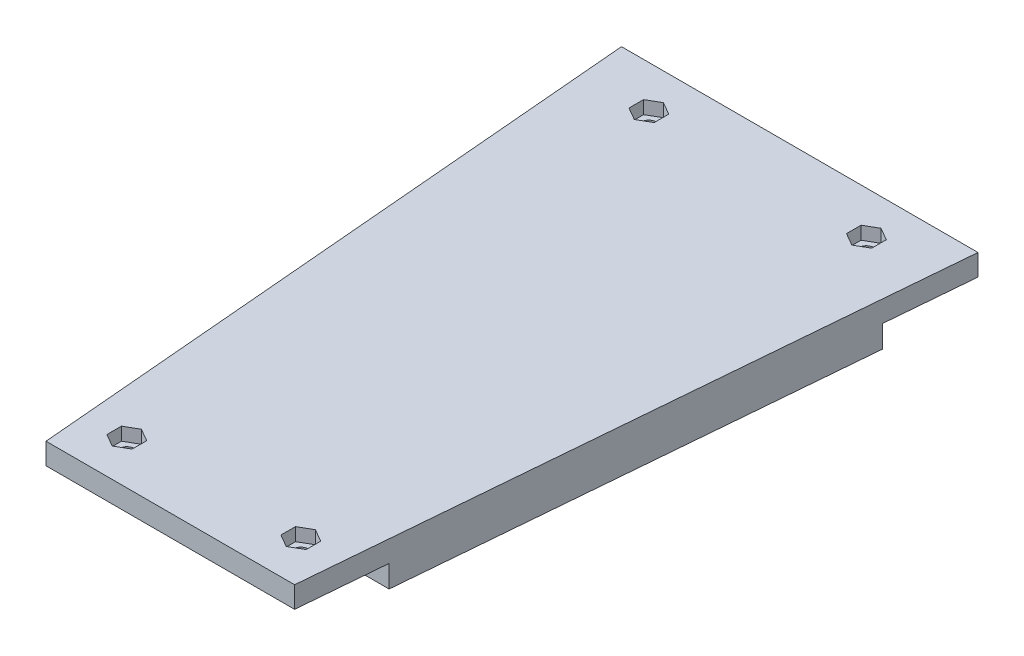
SolidWorks part; units mm, degrees
ref_plane "Front Plane" through (0, 0, 0) normal (0, 0, 1) x (1, 0, 0)
ref_plane "Top Plane" through (0, 0, 0) normal (0, 1, 0) x (1, 0, 0)
ref_plane "Right Plane" through (0, 0, 0) normal (1, 0, 0) x (0, 0, -1)
sketch "Sketch1" plane through (0, 0, 0) normal (0, 1, 0) x (1, 0, 0)
  circle A0 centre (0, 0) radius 50
extrude "Boss-Extrude1" add sketch "Sketch1" along normal blind 10
sketch "Sketch2" plane through (0, 10, 0) normal (0, 1, 0) x (1, 0, 0)
  circle A0 centre (0, 0) radius 20
extrude "Cut-Extrude1" cut sketch "Sketch2" against normal blind 5
sketch "Sketch7" plane through (0, 0, 0) normal (0, -1, 0) x (1, 0, 0)
  line L0 (10.1404, -5.8546) -> (10.1404, -9.1454)
  line L1 (0, 11.7091) -> (2.85, 13.3546)
  line L2 (2.85, 13.3546) -> (2.85, 16.6454)
  line L3 (2.85, 16.6454) -> (0, 18.2909)
  line L4 (0, 18.2909) -> (-2.85, 16.6454)
  line L5 (-2.85, 16.6454) -> (-2.85, 13.3546)
  line L6 (-2.85, 13.3546) -> (0, 11.7091)
  line L7 (10.1404, -9.1454) -> (12.9904, -10.7909)
  line L8 (12.9904, -10.7909) -> (15.8404, -9.1454)
  line L9 (15.8404, -9.1454) -> (15.8404, -5.8546)
  line L10 (15.8404, -5.8546) -> (12.9904, -4.2091)
  line L11 (12.9904, -4.2091) -> (10.1404, -5.8546)
  line L12 (-10.1404, -5.8546) -> (-12.9904, -4.2091)
  line L13 (-12.9904, -4.2091) -> (-15.8404, -5.8546)
  line L14 (-15.8404, -5.8546) -> (-15.8404, -9.1454)
  line L15 (-15.8404, -9.1454) -> (-12.9904, -10.7909)
  line L16 (-12.9904, -10.7909) -> (-10.1404, -9.1454)
  line L17 (-10.1404, -9.1454) -> (-10.1404, -5.8546)
  circle A0 centre (0, 0) radius 15
  circle A1 centre (0, 15) radius 2.85 construction
  point P25 (0, 0)
  dimension "D1" = 3
extrude "Cut-Extrude6" cut sketch "Sketch7" against normal blind 3 contours A0 L2 L3 L4 L5 | L2 A0 L5 L6 L1 | L13 L14 L15 L16 L17 L12 | L10 L11 L0 L7 L8 L9
sketch "Sketch8" plane through (0, 0, 0) normal (0, -1, 0) x (1, 0, 0)
  line L0 (-2.85, 15) -> (2.85, 15) construction
  line L1 (-2.85, 16.6454) -> (-2.85, 13.3546) construction
  line L2 (2.85, 13.3546) -> (2.85, 16.6454) construction
  circle A0 centre (0, 15) radius 1.7
  circle A1 centre (12.9904, -7.5) radius 1.7
  circle A2 centre (-12.9904, -7.5) radius 1.7
  point P14 (0, 0)
  dimension "D1" = 3
extrude "Cut-Extrude7" cut sketch "Sketch8" against normal blind 10
sketch "Sketch9" plane through (0, 0, 0) normal (0, -1, 0) x (1, 0, 0)
  line L1 (-50, 0) -> (50, 0)
  line L2 (-50, 0) -> (-50, 350)
  line L3 (-50, 350) -> (50, 350)
  line L4 (50, 0) -> (50, 350)
  circle A0 centre (0, 0) radius 50 construction
  circle A1 centre (0, 0) radius 50
  circle M23 centre (0, 0) radius 50
  dimension "D1" = 350
extrude "Boss-Extrude3" add sketch "Sketch9" against normal blind 10 separate body contours L4 L3 L2 M23
sketch "Sketch10" plane through (0, 0, 0) normal (0, -1, 0) x (1, 0, 0)
  line L0 (0, 350) -> (0, 0) construction
  line L1 (-50, 350) -> (50, 350) construction
  line L3 (-10.5, 299) -> (10.5, 299)
  line L4 (-10.5, 299) -> (-10.5, 340)
  line L5 (-10.5, 340) -> (10.5, 340)
  line L6 (10.5, 299) -> (10.5, 340)
  line L7 (-10.5, 299) -> (10.5, 340) construction
  line L8 (-10.5, 340) -> (10.5, 299) construction
  point P5 (0, 319.5)
  dimension "D1" = 41
  dimension "D2" = 21
  dimension "D3" = 10
extrude "Cut-Extrude8" cut sketch "Sketch10" against normal blind 10
sketch "Sketch11" plane through (0, 0, 0) normal (0, -1, 0) x (1, 0, 0)
  line L0 (-10.5, 340) -> (-10.5, 299) construction
  line L1 (-10.5, 292.5) -> (10.5, 292.5)
  line L2 (-10.5, 292.5) -> (-10.5, 346.5)
  line L3 (-10.5, 346.5) -> (10.5, 346.5)
  line L4 (10.5, 292.5) -> (10.5, 346.5)
  line L5 (-10.5, 292.5) -> (10.5, 346.5) construction
  line L6 (-10.5, 346.5) -> (10.5, 292.5) construction
  line L7 (-10.5, 340) -> (-10.5, 299)
  line L8 (10.5, 340) -> (-10.5, 340) construction
  line L9 (10.5, 340) -> (-10.5, 340)
  point P0 (0, 319.5)
  point P8 (-10.5, 319.5)
  point P9 (-10.5, 319.5)
  point P11 (0, 346.5)
  point P12 (0, 340)
  line M6 (10.5, 299) -> (-10.5, 299)
  line M8 (-10.5, 340) -> (10.5, 340)
  dimension "D1" = 54
  dimension "D2" = 21
extrude "Cut-Extrude9" cut sketch "Sketch11" against normal blind 1.5 contours L4 L3 L2 M8 | L1 L4 L2 M6
sketch "Sketch12" plane through (0, 1.5, 0) normal (0, -1, 0) x (1, 0, 0)
  line L0 (-5, 343.75) -> (5, 343.75) construction
  line L1 (-10.5, 340) -> (10.5, 340) construction
  line L2 (-10.5, 346.5) -> (10.5, 346.5) construction
  line L3 (-10.5, 346.5) -> (10.5, 346.5)
  line L4 (-10.5, 319.5) -> (10.5, 319.5) construction
  line L5 (-10.5, 346.5) -> (-10.5, 292.5) construction
  line L6 (10.5, 292.5) -> (10.5, 346.5) construction
  circle A0 centre (-5, 343.75) radius 1.7
  circle A1 centre (5, 343.75) radius 1.7
  circle A2 centre (-5, 295.25) radius 1.7
  circle A3 centre (5, 295.25) radius 1.7
  point P3 (0, 343.75)
  point P9 (0, 346.5)
  dimension "D1" = 3.75
extrude "Cut-Extrude10" cut sketch "Sketch12" against normal blind 9 contours A0 | A1 | A2 | A3
sketch "Sketch13" plane through (0, 0, 0) normal (0, -1, 0) x (1, 0, 0)
  line L0 (-50, 0) -> (-20, 350)
  line L1 (0, 350) -> (0, 0) construction
  line L2 (50, 0) -> (20, 350)
  line L3 (50, 0) -> (50, 350)
  line L4 (50, 350) -> (-50, 350)
  line L5 (-50, 350) -> (-50, 0)
  line L6 (50, 0) -> (50, 350)
  line L7 (50, 350) -> (-50, 350)
  line L8 (-50, 350) -> (-50, 0)
  arc A1 (50, 0) -> (-50, 0) centre (0, 0) ccw
  arc A2 (50, 0) -> (-50, 0) centre (0, 0) ccw
  arc M7 (-50, 0) -> (50, 0) centre (0, 0) cw
  line M8 (50, 0) -> (50, 350)
  line M9 (50, 350) -> (-50, 350)
  line M10 (-50, 350) -> (-50, 0)
  dimension "D2" = 20
  dimension "D1" = 0
extrude "Cut-Extrude11" cut sketch "Sketch13" against normal blind 10 contours L0 M7 M9 M10 | L2 M7 M8 M9
sketch "Sketch14" plane through (0, 0, 0) normal (0, -1, 0) x (1, 0, 0)
  line L0 (0, 0) -> (0, 125) construction
  line L2 (-64.1644, 125) -> (57.7014, 125)
  line L3 (-64.1644, 125) -> (-64.1644, 375)
  line L4 (-64.1644, 375) -> (57.7014, 375)
  line L5 (57.7014, 125) -> (57.7014, 375)
  point P7 (0, 0)
  dimension "D1" = 125
  dimension "D2" = 250
sketch "Sketch15" plane through (0, 10, 0) normal (0, 1, 0) x (1, 0, 0)
  line L1 (57.7014, -125) -> (-74.0337, -125)
  line L2 (57.7014, -125) -> (57.7014, 54.2666)
  line L3 (57.7014, 54.2666) -> (-74.0337, 54.2666)
  line L4 (-74.0337, -125) -> (-74.0337, 54.2666)
extrude "Cut-Extrude12" cut sketch "Sketch15" against normal blind 79
sketch "Sketch16" plane through (0, 10, 0) normal (0, 1, 0) x (1, 0, 0)
  line L0 (-40.9724, -105.3222) -> (-37.599, -144.6778)
  line L2 (-39.2857, -125) -> (-20, -350) construction
  line L3 (0, -125) -> (0, -150.7956) construction
  line L4 (40.9724, -105.3222) -> (37.599, -144.6778)
  line L5 (-40.9724, -105.3222) -> (40.9724, -105.3222)
  line L9 (20, -350) -> (39.2857, -125)
  line L10 (39.2857, -125) -> (-39.2857, -125)
  line L11 (-39.2857, -125) -> (-20, -350)
  line L12 (-20, -350) -> (20, -350)
  line L13 (20, -350) -> (39.2857, -125)
  line L14 (39.2857, -125) -> (-39.2857, -125)
  line L15 (-39.2857, -125) -> (-20, -350)
  line L16 (-20, -350) -> (20, -350)
  point P4 (-39.2857, -125)
  line M18 (39.2857, -125) -> (-39.2857, -125)
  dimension "D1" = 0
extrude "Boss-Extrude4" add sketch "Sketch16" against normal blind 4.9 contours L5 L0 L14 L4 M18
sketch "Sketch17" plane through (0, 5.1, 0) normal (0, -1, 0) x (1, 0, 0)
  line L0 (0, 125) -> (0, 115) construction
  line L1 (0, 0) -> (0, 125) construction
  line L2 (-25, 115) -> (25, 115) construction
  circle A0 centre (-25, 115) radius 1.7
  circle A1 centre (25, 115) radius 1.7
  point P8 (0, 115)
extrude "Cut-Extrude13" cut sketch "Sketch17" against normal blind 10
sketch "Sketch18" plane through (0, 10, 0) normal (0, 1, 0) x (1, 0, 0)
  line L0 (0, -105.3222) -> (0, -125) construction
  line L1 (-25, -111.6514) -> (-27.9, -113.3257)
  line L2 (-27.9, -113.3257) -> (-27.9, -116.6743)
  line L3 (-27.9, -116.6743) -> (-25, -118.3486)
  line L4 (-25, -118.3486) -> (-22.1, -116.6743)
  line L5 (-22.1, -116.6743) -> (-22.1, -113.3257)
  line L6 (-22.1, -113.3257) -> (-25, -111.6514)
  line L7 (-40.9724, -105.3222) -> (40.9724, -105.3222) construction
  line L8 (22.1, -113.3257) -> (25, -111.6514)
  line L9 (22.1, -116.6743) -> (22.1, -113.3257)
  line L10 (25, -118.3486) -> (22.1, -116.6743)
  line L11 (27.9, -116.6743) -> (25, -118.3486)
  line L12 (27.9, -113.3257) -> (27.9, -116.6743)
  line L13 (25, -111.6514) -> (27.9, -113.3257)
  circle A0 centre (-25, -115) radius 2.9 construction
  circle A1 centre (25, -115) radius 2.9 construction
extrude "Cut-Extrude14" cut sketch "Sketch18" against normal blind 3
sketch "Sketch19" plane through (0, 0, 125) normal (0, 0, -1) x (-1, 0, 0)
  line L4 (39.2857, 5.1) -> (-39.2857, 5.1)
  line L5 (-39.2857, 5.1) -> (-39.2857, 0)
  line L6 (-39.2857, 0) -> (39.2857, 0)
  line L7 (39.2857, 0) -> (39.2857, 5.1)
  line L8 (39.2857, 5.1) -> (-39.2857, 5.1)
  line L9 (-39.2857, 5.1) -> (-39.2857, 0)
  line L10 (-39.2857, 0) -> (39.2857, 0)
  line L11 (39.2857, 0) -> (39.2857, 5.1)
  dimension "D1" = 0
extrude "Cut-Extrude15" cut sketch "Sketch19" against normal blind 0.5
sketch "Sketch20" plane through (0, 0, 0) normal (0, -1, 0) x (1, 0, 0)
  line L0 (-20, 350) -> (20, 350) construction
  line L1 (-45.6201, 364.5287) -> (46.9916, 364.5287)
  line L2 (-45.6201, 364.5287) -> (-45.6201, 250)
  line L3 (-45.6201, 250) -> (46.9916, 250)
  line L4 (46.9916, 364.5287) -> (46.9916, 250)
  dimension "D1" = 100
extrude "Cut-Extrude16" cut sketch "Sketch20" against normal blind 10 contours L2 L1 L4 L3
sketch "Sketch21" plane through (0, 0, 0) normal (0, -1, 0) x (1, 0, 0)
  line L0 (-30.2857, 230) -> (30.2857, 230)
  line L4 (28.5714, 250) -> (-28.5714, 250)
  line L5 (-28.5714, 250) -> (-39.2429, 125.5)
  line L6 (-39.2429, 125.5) -> (39.2429, 125.5)
  line L7 (39.2429, 125.5) -> (28.5714, 250)
  line L8 (28.5714, 250) -> (-28.5714, 250)
  line L9 (-28.5714, 250) -> (-39.2429, 125.5)
  line L10 (-39.2429, 125.5) -> (39.2429, 125.5)
  line L11 (39.2429, 125.5) -> (28.5714, 250)
  line M6 (28.5714, 250) -> (-28.5714, 250)
  line M7 (-28.5714, 250) -> (-39.2429, 125.5)
  line M9 (39.2429, 125.5) -> (28.5714, 250)
  dimension "D2" = 20
  dimension "D1" = 0
extrude "Cut-Extrude17" cut sketch "Sketch21" against normal blind 5.1 contours L0 M7 M9 M6
sketch "Sketch22" plane through (0, 5.1, 0) normal (0, -1, 0) x (1, 0, 0)
  line L0 (0, 250) -> (0, 230) construction
  line L1 (28.5714, 250) -> (-28.5714, 250) construction
  line L2 (-30.2857, 230) -> (30.2857, 230) construction
  line L3 (-20, 240) -> (20, 240) construction
  circle A0 centre (-20, 240) radius 1.7
  circle A1 centre (20, 240) radius 1.7
  point P9 (0, 240)
  dimension "D1" = 40
extrude "Cut-Extrude18" cut sketch "Sketch22" against normal blind 5.1
sketch "Sketch23" plane through (0, 10, 0) normal (0, 1, 0) x (1, 0, 0)
  line L0 (0, -250) -> (0, -230.1141) construction
  line L1 (-20, -236.6514) -> (-22.9, -238.3257)
  line L2 (-22.9, -238.3257) -> (-22.9, -241.6743)
  line L3 (-22.9, -241.6743) -> (-20, -243.3486)
  line L4 (-20, -243.3486) -> (-17.1, -241.6743)
  line L5 (-17.1, -241.6743) -> (-17.1, -238.3257)
  line L6 (-17.1, -238.3257) -> (-20, -236.6514)
  line L7 (-28.5714, -250) -> (28.5714, -250) construction
  line L8 (17.1, -238.3257) -> (20, -236.6514)
  line L9 (17.1, -241.6743) -> (17.1, -238.3257)
  line L10 (20, -243.3486) -> (17.1, -241.6743)
  line L11 (22.9, -241.6743) -> (20, -243.3486)
  line L12 (22.9, -238.3257) -> (22.9, -241.6743)
  line L13 (20, -236.6514) -> (22.9, -238.3257)
  circle A0 centre (-20, -240) radius 2.9 construction
  circle A1 centre (20, -240) radius 2.9 construction
extrude "Cut-Extrude19" cut sketch "Sketch23" against normal blind 3
